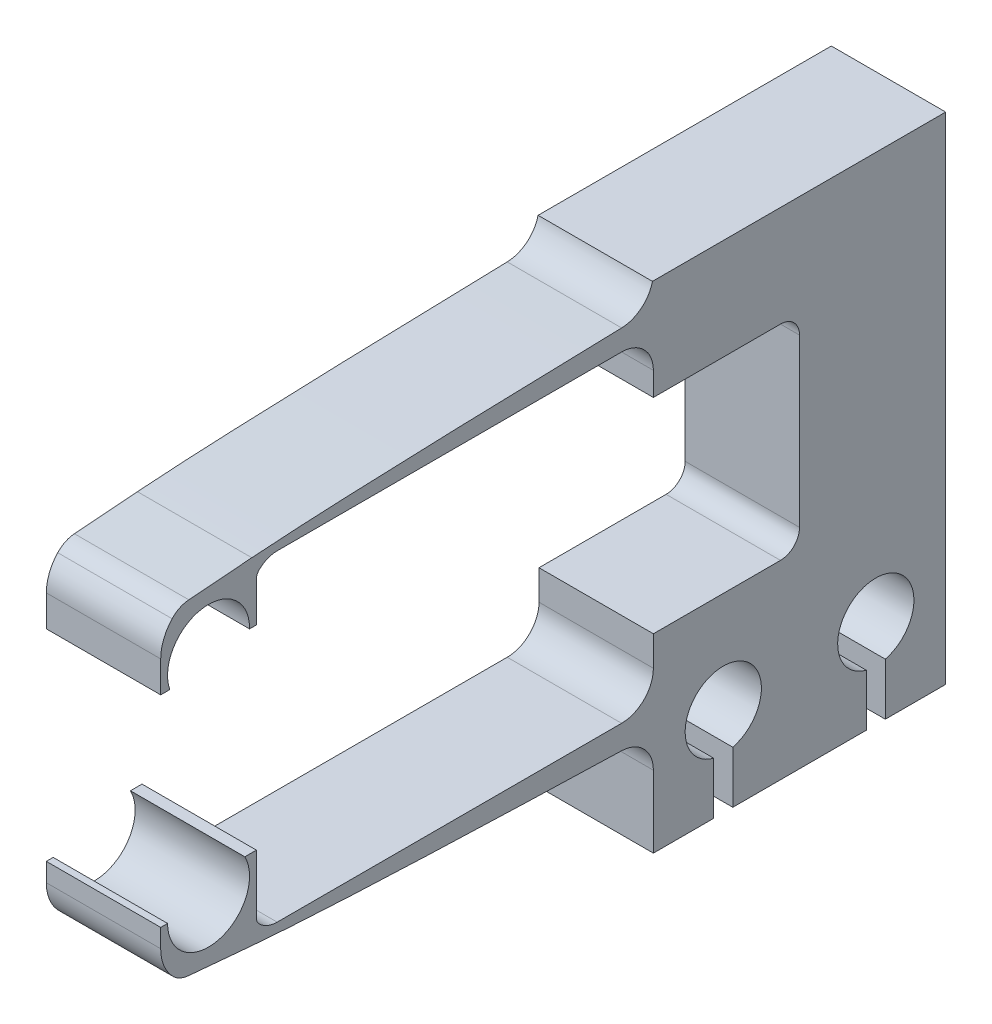
SolidWorks part; units mm, degrees
material "Titanium"
ref_plane "Front" through (0, 0, 0) normal (0, 0, 1) x (1, 0, 0)
ref_plane "Top" through (0, 0, 0) normal (0, 1, 0) x (1, 0, 0)
ref_plane "Right" through (0, 0, 0) normal (1, 0, 0) x (0, 0, -1)
sketch "Sketch1" plane through (0, 0, 0) normal (1, 0, 0) x (0, 0, -1)
  line L0 (0, 0) -> (23.25, 0) construction
  line L1 (1.7, 6.2) -> (16.25, 6.2) construction
  line L2 (-1.7, -4.45) -> (-1.7, -6.45) construction
  line L3 (0, -6.45) -> (-1.7, -6.45) construction
  line L4 (41.8092, -4.5) -> (-22.3482, -4.5) construction
  line L6 (43.4192, 4.5) -> (-21.0309, 4.5) construction
  line L7 (17.5, 4.025) -> (17.5, 4.95)
  line L8 (0, -2.75) -> (0, 2.5) construction
  line L9 (17.5, -5.2) -> (17.5, -8.6732)
  line L10 (17.5, -4.025) -> (17.5, -5.2)
  line L11 (-1.7, 4.2) -> (-1.7, 6.2) construction
  line L12 (1.7, -4.45) -> (1.7, -6.45) construction
  line L13 (1.7, -6.45) -> (16.25, -6.45) construction
  line L14 (16.25, -6.45) -> (16.25, -7.3867) construction
  line L15 (17.5, 8.5) -> (29, 8.5)
  line L16 (-1.7, 6.2) -> (0, 6.2) construction
  line L17 (29, -11.5) -> (17.5, -11.5)
  line L18 (1.7, 4.2) -> (1.7, 6.2) construction
  line L19 (17.5, 8.3014) -> (17.5, 8.5)
  line L20 (17.5, 4.95) -> (17.5, 8.3014)
  line L21 (17.5, -4.025) -> (23.25, -4.025)
  line L25 (17.5, -8.6732) -> (17.5, -11.5)
  line L26 (29, 8.5) -> (29, -11.5)
  line L27 (23.25, 0) -> (29, 0) construction
  line L29 (0, -4.45) -> (0, -6.45) construction
  line L30 (23.25, -4.025) -> (23.25, 4.025)
  line L31 (23.25, 4.025) -> (17.5, 4.025)
  arc A1 (16.25, -6.45) -> (17.5, -5.2) centre (16.25, -5.2) ccw construction
  arc A2 (-1.7, -4.45) -> (1.7, -4.45) centre (0, -4.45) cw construction
  arc A3 (1.7, 4.2) -> (-1.7, 4.2) centre (0, 4.2) cw construction
  arc A4 (16.25, 6.2) -> (17.5, 4.95) centre (16.25, 4.95) cw construction
  arc A5 (16.25, -7.3867) -> (17.5, -8.6732) centre (16.2129, -8.6732) cw construction
  arc A9 (16.25, 7.0194) -> (17.5, 8.3014) centre (16.2177, 8.3014) ccw construction
  spline S0 degree 4 poles (17.8857, -7.4327) (17.7428, -7.4287) (17.6099, -7.4252) (17.1374, -7.412) (16.4075, -7.3913) (15.697, -7.3708) (14.3979, -7.3322) (13.3617, -7.2996) (12.1009, -7.2589) (10.9759, -7.2202) (9.7686, -7.1769) (8.6115, -7.1325) (7.424, -7.084) (6.2553, -7.0321) (5.0754, -6.975) (3.903, -6.9111) (2.7276, -6.8374) (1.7227, -6.7597) (0.9543, -6.6832) (0.4564, -6.6106) (0.2371, -6.5651) (0.1371, -6.537) (0.0873, -6.5192) (0.0601, -6.5073) (0.043, -6.4984) (0.0307, -6.4909) (0.016, -6.4805) (0.0052, -6.4697) (0.0008, -6.459) (0, -6.45) knots 0 0 0 0 0 0.022654 0.045309 0.090617 0.156222 0.221826 0.28743 0.353034 0.418638 0.484242 0.549846 0.61545 0.681055 0.746659 0.812263 0.877867 0.943221 0.971682 0.984223 0.9901 0.993094 0.99484 0.995992 0.996719 0.997393 0.99806 1 1 1 1 1 construction
  spline S1 degree 4 poles (16.25, -7.3867) (15.9825, -7.379) (15.4539, -7.3636) (14.3979, -7.3322) (13.3617, -7.2996) (12.1009, -7.2589) (10.9759, -7.2202) (9.7686, -7.1769) (8.6115, -7.1325) (7.424, -7.084) (6.2553, -7.0321) (5.0754, -6.975) (3.903, -6.9111) (2.7276, -6.8374) (1.7227, -6.7597) (0.9543, -6.6832) (0.4564, -6.6106) (0.2371, -6.5651) (0.1371, -6.537) (0.0873, -6.5192) (0.0601, -6.5073) (0.043, -6.4984) (0.0307, -6.4909) (0.016, -6.4805) (0.0052, -6.4697) (0.0008, -6.459) (0, -6.45) knots 0.090617 0.090617 0.090617 0.090617 0.090617 0.156222 0.221826 0.28743 0.353034 0.418638 0.484242 0.549846 0.61545 0.681055 0.746659 0.812263 0.877867 0.943221 0.971682 0.984223 0.9901 0.993094 0.99484 0.995992 0.996719 0.997393 0.99806 1 1 1 1 1 construction
  spline S2 degree 4 poles (17.8845, 7.0597) (17.7463, 7.0563) (17.6049, 7.053) (17.143, 7.0417) (16.4101, 7.0236) (15.7139, 7.0059) (14.431, 6.9726) (13.4161, 6.9447) (12.1774, 6.9098) (11.0741, 6.8767) (9.8887, 6.8398) (8.7532, 6.8019) (7.5875, 6.7607) (6.4405, 6.7167) (5.2822, 6.6684) (4.1313, 6.6148) (2.9761, 6.5533) (1.9352, 6.4867) (1.1121, 6.4193) (0.5505, 6.3551) (0.2629, 6.3064) (0.1449, 6.2783) (0.0901, 6.2616) (0.0611, 6.2506) (0.0435, 6.2426) (0.031, 6.236) (0.0166, 6.227) (0.0056, 6.2178) (0.001, 6.2082) (0, 6.2) knots 0 0 0 0 0 0.02267 0.045339 0.090679 0.155107 0.219536 0.283964 0.348393 0.412821 0.47725 0.541678 0.606107 0.670535 0.734964 0.799392 0.863821 0.928249 0.967999 0.98346 0.99001 0.993269 0.995073 0.996228 0.996923 0.997583 0.998234 1 1 1 1 1 construction
  spline S3 degree 4 poles (16.25, 7.0194) (15.9875, 7.0128) (15.4701, 6.9996) (14.431, 6.9726) (13.4161, 6.9447) (12.1774, 6.9098) (11.0741, 6.8767) (9.8887, 6.8398) (8.7532, 6.8019) (7.5875, 6.7607) (6.4405, 6.7167) (5.2822, 6.6684) (4.1313, 6.6148) (2.9761, 6.5533) (1.9352, 6.4867) (1.1121, 6.4193) (0.5505, 6.3551) (0.2629, 6.3064) (0.1449, 6.2783) (0.0901, 6.2616) (0.0611, 6.2506) (0.0435, 6.2426) (0.031, 6.236) (0.0166, 6.227) (0.0056, 6.2178) (0.001, 6.2082) (0, 6.2) knots 0.090679 0.090679 0.090679 0.090679 0.090679 0.155107 0.219536 0.283964 0.348393 0.412821 0.47725 0.541678 0.606107 0.670535 0.734964 0.799392 0.863821 0.928249 0.967999 0.98346 0.99001 0.993269 0.995073 0.996228 0.996923 0.997583 0.998234 1 1 1 1 1 construction
  point P26 (0, -0.125)
  dimension "D7" = 1.75
  dimension "D13" = 8.05
  dimension "D14" = 2
  dimension "D2" = 1.7
  dimension "D9" = 8.5
  dimension "D11" = 4.5
  dimension "D12" = 4.5
  dimension "D8" = 5.75
  dimension "D4" = 17.5
  dimension "D3" = 2
  dimension "D5" = 23.25
  dimension "D6" = 16.25
  dimension "D10" = 11.5
  dimension "D15" = 2
  dimension "D16" = 16.25
extrude "Boss-Extrude1" add sketch "Sketch1" along normal mid plane 4.5
sketch "Sketch4" plane through (-2.25, 0, 0) normal (-1, 0, 0) x (0, 0, 1)
  line L0 (-26.625, -11.5) -> (-26.625, -9.4524)
  line L1 (-17.5, -11.5) -> (-29, -11.5) construction
  line L2 (-26.625, -11.5) -> (-25.875, -11.5)
  line L3 (-25.875, -11.5) -> (-25.875, -9.4524)
  line L4 (-20.625, -9.4524) -> (-20.625, -11.5)
  line L5 (-20.625, -11.5) -> (-19.875, -11.5)
  line L6 (-19.875, -11.5) -> (-19.875, -9.4524)
  line L7 (-26.625, -9.4524) -> (-25.875, -9.4524) construction
  line L8 (-20.625, -9.4524) -> (-19.875, -9.4524) construction
  line L9 (-20.25, -8) -> (-26.25, -8) construction
  line L10 (-26.25, -8) -> (-26.25, 0) construction
  line L11 (-26.25, 0) -> (-23.25, 0) construction
  line L12 (-23.25, 4.025) -> (-23.25, -4.025) construction
  line L13 (-17.5, -4.025) -> (-17.5, -11.5) construction
  line L14 (-29, -11.5) -> (-29, 8.5) construction
  arc A0 (-26.625, -9.4524) -> (-25.875, -9.4524) centre (-26.25, -8) cw
  arc A1 (-20.625, -9.4524) -> (-19.875, -9.4524) centre (-20.25, -8) cw
  dimension "D5" = 1.5
  dimension "D1" = 0.75
  dimension "D2" = 3
  dimension "D3" = 8
  dimension "D4" = 6
  dimension "D6" = 2.75
  dimension "D7" = 2.75
extrude "Cut-Extrude1" cut sketch "Sketch4" against normal through all
fillet "Fillet1" radius 0.75 2 edges at (0, -4.025, -23.25) (0, 4.025, -23.25)
sketch "Sketch2" plane through (0, 0, 0) normal (1, 0, 0) x (0, 0, -1)
  line L0 (1.7, -6.45) -> (16.25, -6.45) construction
  line L1 (1.7, -4.45) -> (1.7, -6.45) construction
  line L2 (-1.7, -4.45) -> (-1.7, -6.45) construction
  line L3 (0, -6.45) -> (-1.7, -6.45) construction
  line L5 (1.7, -6.45) -> (16.25, -6.45)
  line L6 (1.7, -4.45) -> (1.7, -6.45)
  line L7 (-1.7, -4.45) -> (-1.7, -6.45)
  line L8 (0, -6.45) -> (-1.7, -6.45)
  line L9 (17.5, -5.2) -> (17.5, -8.6732) construction
  line L11 (17.5, -5.2) -> (17.5, -8.6732)
  line L12 (17.5, 4.95) -> (17.5, 8.3014) construction
  line L13 (1.7, 6.2) -> (16.25, 6.2) construction
  line L14 (-1.7, 6.2) -> (0, 6.2) construction
  line L15 (-1.7, 4.2) -> (-1.7, 6.2) construction
  line L16 (1.7, 4.2) -> (1.7, 6.2) construction
  line L17 (17.5, 4.95) -> (17.5, 8.3014)
  line L18 (1.7, 6.2) -> (16.25, 6.2)
  line L19 (-1.7, 6.2) -> (0, 6.2)
  line L20 (-1.7, 4.2) -> (-1.7, 6.2)
  line L21 (1.7, 4.2) -> (1.7, 6.2)
  arc A0 (1.7, -4.45) -> (-1.7, -4.45) centre (0, -4.45) ccw construction
  arc A3 (1.7, -4.45) -> (-1.7, -4.45) centre (0, -4.45) ccw
  arc A4 (17.5, -8.6732) -> (16.25, -7.3867) centre (16.2129, -8.6732) ccw construction
  arc A5 (16.25, -6.45) -> (17.5, -5.2) centre (16.25, -5.2) ccw construction
  arc A6 (16.25, -6.45) -> (17.5, -5.2) centre (16.25, -5.2) ccw
  arc A7 (17.5, -8.6732) -> (16.25, -7.3867) centre (16.2129, -8.6732) ccw
  arc A8 (16.25, 7.0194) -> (17.5, 8.3014) centre (16.2177, 8.3014) ccw construction
  arc A9 (17.5, 4.95) -> (16.25, 6.2) centre (16.25, 4.95) ccw construction
  arc A10 (-1.7, 4.2) -> (1.7, 4.2) centre (0, 4.2) ccw construction
  arc A11 (16.25, 7.0194) -> (17.5, 8.3014) centre (16.2177, 8.3014) ccw
  arc A12 (17.5, 4.95) -> (16.25, 6.2) centre (16.25, 4.95) ccw
  arc A13 (-1.7, 4.2) -> (1.7, 4.2) centre (0, 4.2) ccw
  spline S0 degree 4 poles (1015.806, -36.1419) (-25.1587, -6.1713) (25.4391, -7.6458) (16.9585, -7.4127) (13.3617, -7.2996) (12.1009, -7.2589) (10.9759, -7.2202) (9.7686, -7.1769) (8.6115, -7.1325) (7.424, -7.084) (6.2553, -7.0321) (5.0754, -6.975) (3.903, -6.9111) (2.7276, -6.8374) (1.7227, -6.7597) (0.9543, -6.6832) (0.4564, -6.6106) (0.2371, -6.5651) (0.1371, -6.537) (0.0873, -6.5192) (0.0601, -6.5073) (0.043, -6.4984) (0.0307, -6.4909) (-0.1968, -6.3287) (0.0146, -5.4129) (43.0294, 6.1836) (-939.7828, -347.8084) knots -0.557828 -0.557828 -0.557828 -0.557828 -0.557828 0.156222 0.221826 0.28743 0.353034 0.418638 0.484242 0.549846 0.61545 0.681055 0.746659 0.812263 0.877867 0.943221 0.971682 0.984223 0.9901 0.993094 0.99484 0.995992 0.996719 0.997393 0.99806 1.058105 1.058105 1.058105 1.058105 1.058105 only from (16.25, -7.3867) to (0, -6.45) construction
  spline S1 degree 4 poles (16.25, -7.3867) (15.9825, -7.379) (15.4539, -7.3636) (14.3979, -7.3322) (13.3617, -7.2996) (12.1009, -7.2589) (10.9759, -7.2202) (9.7686, -7.1769) (8.6115, -7.1325) (7.424, -7.084) (6.2553, -7.0321) (5.0754, -6.975) (3.903, -6.9111) (2.7276, -6.8374) (1.7227, -6.7597) (0.9543, -6.6832) (0.4564, -6.6106) (0.2371, -6.5651) (0.1371, -6.537) (0.0873, -6.5192) (0.0601, -6.5073) (0.043, -6.4984) (0.0307, -6.4909) (0.016, -6.4805) (0.0052, -6.4697) (0.0008, -6.459) (0, -6.45) knots 0.090617 0.090617 0.090617 0.090617 0.090617 0.156222 0.221826 0.28743 0.353034 0.418638 0.484242 0.549846 0.61545 0.681055 0.746659 0.812263 0.877867 0.943221 0.971682 0.984223 0.9901 0.993094 0.99484 0.995992 0.996719 0.997393 0.99806 1 1 1 1 1
  spline S2 degree 4 poles (1015.9078, 32.1833) (-25.0126, 5.9604) (25.309, 7.2431) (16.9336, 7.0414) (13.4161, 6.9447) (12.1774, 6.9098) (11.0741, 6.8767) (9.8887, 6.8398) (8.7532, 6.8019) (7.5875, 6.7607) (6.4405, 6.7167) (5.2822, 6.6684) (4.1313, 6.6148) (2.9761, 6.5533) (1.9352, 6.4867) (1.1121, 6.4193) (0.5505, 6.3551) (0.2629, 6.3064) (0.1449, 6.2783) (0.0901, 6.2616) (0.0611, 6.2506) (0.0435, 6.2426) (0.031, 6.236) (-0.1871, 6.1007) (-0.1475, 5.3114) (43.6109, -10.4306) (-899.4391, 442.7049) knots -0.544854 -0.544854 -0.544854 -0.544854 -0.544854 0.155107 0.219536 0.283964 0.348393 0.412821 0.47725 0.541678 0.606107 0.670535 0.734964 0.799392 0.863821 0.928249 0.967999 0.98346 0.99001 0.993269 0.995073 0.996228 0.996923 0.997583 0.998234 1.053425 1.053425 1.053425 1.053425 1.053425 only from (16.25, 7.0194) to (0, 6.2) construction
  spline S3 degree 4 poles (16.25, 7.0194) (15.9875, 7.0128) (15.4701, 6.9996) (14.431, 6.9726) (13.4161, 6.9447) (12.1774, 6.9098) (11.0741, 6.8767) (9.8887, 6.8398) (8.7532, 6.8019) (7.5875, 6.7607) (6.4405, 6.7167) (5.2822, 6.6684) (4.1313, 6.6148) (2.9761, 6.5533) (1.9352, 6.4867) (1.1121, 6.4193) (0.5505, 6.3551) (0.2629, 6.3064) (0.1449, 6.2783) (0.0901, 6.2616) (0.0611, 6.2506) (0.0435, 6.2426) (0.031, 6.236) (0.0166, 6.227) (0.0056, 6.2178) (0.001, 6.2082) (0, 6.2) knots 0.090679 0.090679 0.090679 0.090679 0.090679 0.155107 0.219536 0.283964 0.348393 0.412821 0.47725 0.541678 0.606107 0.670535 0.734964 0.799392 0.863821 0.928249 0.967999 0.98346 0.99001 0.993269 0.995073 0.996228 0.996923 0.997583 0.998234 1 1 1 1 1
extrude "Boss-Extrude2" add sketch "Sketch2" along normal mid plane 4.5
sketch "Sketch3" plane through (-2.25, 0, 0) normal (-1, 0, 0) x (0, 0, 1)
  line L0 (1.7, -6.45) -> (-1.6908, -6.7522)
  line L1 (1.7, -6.45) -> (0, -6.45) construction
  line L2 (1.7, -6.45) -> (0, -6.45)
  line L3 (0, 6.2) -> (1.7, 6.2) construction
  line L4 (0, 6.2) -> (1.7, 6.2)
  line L5 (1.7, 6.2) -> (-1.7017, 6.4652)
  spline S0 degree 4 poles (939.596, -347.7411) (-43.0233, 6.1819) (-0.0146, -5.413) (0.1968, -6.3287) (-0.0307, -6.4909) (-0.043, -6.4984) (-0.0601, -6.5073) (-0.0873, -6.5192) (-0.1371, -6.537) (-0.2371, -6.5651) (-0.4564, -6.6106) (-0.9543, -6.6832) (-1.7227, -6.7597) (-2.7276, -6.8374) (-3.903, -6.9111) (-5.0754, -6.975) (-6.2553, -7.0321) (-7.424, -7.084) (-8.6115, -7.1325) (-9.7686, -7.1769) (-10.9759, -7.2202) (-12.1009, -7.2589) (-13.3617, -7.2996) (-16.9585, -7.4127) (-25.4391, -7.6458) (25.1593, -6.1713) (-1015.825, -36.1424) knots 0.032516 0.032516 0.032516 0.032516 0.032516 0.092558 0.093225 0.093899 0.094625 0.095777 0.097523 0.100517 0.106395 0.118935 0.147397 0.212751 0.278355 0.343959 0.409563 0.475167 0.540771 0.606375 0.671979 0.737584 0.803188 0.868792 0.934396 1.648448 1.648448 1.648448 1.648448 1.648448 only from (0, -6.45) to (-16.25, -7.3867) construction
  spline S1 degree 4 poles (0, -6.45) (-0.0008, -6.459) (-0.0052, -6.4697) (-0.016, -6.4805) (-0.0307, -6.4909) (-0.043, -6.4984) (-0.0601, -6.5073) (-0.0873, -6.5192) (-0.1371, -6.537) (-0.2371, -6.5651) (-0.4564, -6.6106) (-0.8426, -6.6669) (-1.2048, -6.7069) (-1.5113, -6.7362) (-1.6908, -6.7522) knots 0.090617 0.090617 0.090617 0.090617 0.090617 0.092558 0.093225 0.093899 0.094625 0.095777 0.097523 0.100517 0.106395 0.118935 0.147397 0.187581 0.187581 0.187581 0.187581 0.187581
  spline S2 degree 4 poles (0, -6.45) (-0.0008, -6.459) (-0.0052, -6.4697) (-0.016, -6.4805) (-0.0307, -6.4909) (-0.043, -6.4984) (-0.0601, -6.5073) (-0.0873, -6.5192) (-0.1371, -6.537) (-0.2371, -6.5651) (-0.4564, -6.6106) (-0.9543, -6.6832) (-1.7227, -6.7597) (-2.7276, -6.8374) (-3.903, -6.9111) (-5.0754, -6.975) (-6.2553, -7.0321) (-7.424, -7.084) (-8.6115, -7.1325) (-9.7686, -7.1769) (-10.9759, -7.2202) (-12.1009, -7.2589) (-13.3617, -7.2996) (-14.3979, -7.3322) (-15.4539, -7.3636) (-15.9825, -7.379) (-16.25, -7.3867) knots 0.090617 0.090617 0.090617 0.090617 0.090617 0.092558 0.093225 0.093899 0.094625 0.095777 0.097523 0.100517 0.106395 0.118935 0.147397 0.212751 0.278355 0.343959 0.409563 0.475167 0.540771 0.606375 0.671979 0.737584 0.803188 0.868792 0.934396 1 1 1 1 1 construction
  spline S3 degree 4 poles (-1015.9078, 32.1833) (25.0126, 5.9604) (-25.309, 7.2431) (-16.9336, 7.0414) (-13.4161, 6.9447) (-12.1774, 6.9098) (-11.0741, 6.8767) (-9.8887, 6.8398) (-8.7532, 6.8019) (-7.5875, 6.7607) (-6.4405, 6.7167) (-5.2822, 6.6684) (-4.1313, 6.6148) (-2.9761, 6.5533) (-1.9352, 6.4867) (-1.1121, 6.4193) (-0.5505, 6.3551) (-0.2629, 6.3064) (-0.1449, 6.2783) (-0.0901, 6.2616) (-0.0611, 6.2506) (-0.0435, 6.2426) (-0.031, 6.236) (0.1871, 6.1007) (0.1475, 5.3114) (-43.6109, -10.4306) (899.4391, 442.7049) knots -0.544854 -0.544854 -0.544854 -0.544854 -0.544854 0.155107 0.219536 0.283964 0.348393 0.412821 0.47725 0.541678 0.606107 0.670535 0.734964 0.799392 0.863821 0.928249 0.967999 0.98346 0.99001 0.993269 0.995073 0.996228 0.996923 0.997583 0.998234 1.053425 1.053425 1.053425 1.053425 1.053425 only from (-16.25, 7.0194) to (0, 6.2) construction
  spline S4 degree 4 poles (-1.7017, 6.4652) (-1.5885, 6.4564) (-1.2977, 6.4327) (-0.9381, 6.3994) (-0.5505, 6.3551) (-0.2629, 6.3064) (-0.1449, 6.2783) (-0.0901, 6.2616) (-0.0611, 6.2506) (-0.0435, 6.2426) (-0.031, 6.236) (-0.0166, 6.227) (-0.0056, 6.2178) (-0.001, 6.2082) (0, 6.2) knots 0.902915 0.902915 0.902915 0.902915 0.902915 0.928249 0.967999 0.98346 0.99001 0.993269 0.995073 0.996228 0.996923 0.997583 0.998234 1 1 1 1 1
extrude "Boss-Extrude4" add sketch "Sketch3" against normal through all
fillet "Fillet2" radius 1 4 edges at (0, -6.45, -1.7) (0, -6.45, 1.7) (0, 6.2, 1.7) (0, 6.2, -1.7)
sketch "Sketch6" plane through (0, 0, 0) normal (1, 0, 0) x (0, 0, -1)
  line L0 (-1.6125, -4.3375) -> (-1.6963, -4.3375)
  line L1 (-1.6963, -4.3375) -> (-1.6963, -2.65)
  line L2 (-1.6963, -2.65) -> (1.6963, -2.65)
  line L3 (1.6963, -2.65) -> (1.6963, -4.3375)
  line L4 (1.6963, -4.3375) -> (1.6125, -4.3375)
  line L5 (0, -2.75) -> (0, -2.65) construction
  line L6 (1.6122, 4.0837) -> (1.696, 4.0837)
  line L7 (1.696, 4.0837) -> (1.696, 2.3962)
  line L8 (1.696, 2.3962) -> (-1.696, 2.3962)
  line L9 (-1.696, 2.3962) -> (-1.696, 4.0837)
  line L10 (-1.696, 4.0837) -> (-1.6122, 4.0837)
  line L11 (0, -4.3375) -> (0, -4.45) construction
  arc A0 (1.6122, 4.0837) -> (-1.6122, 4.0837) centre (0, 4.1125) ccw
  arc A1 (-1.6125, -4.3375) -> (1.6125, -4.3375) centre (0, -4.3375) ccw
  arc A2 (1.7, -4.45) -> (-1.7, -4.45) centre (0, -4.45) ccw construction
  arc A3 (-1.7, 4.2) -> (1.7, 4.2) centre (0, 4.2) ccw construction
  circle A4 centre (0, -4.3375) radius 1.5875 construction
  point P7 (0, -2.75)
  point P9 (0, 2.5)
  dimension "D1" = 0.025
  dimension "D3" = 3.175
  dimension "D2" = 0.1
  dimension "D4" = 0.0838
extrude "Cut-Extrude4" cut sketch "Sketch6" against normal mid plane 10
sketch "Sketch5" [suppressed] plane through (-2.25, 0, 0) normal (-1, 0, 0) x (0, 0, 1)
  line L1 (-18.5, 0) -> (31.5, 0)
  line L2 (-18.5, 0) -> (-18.5, -11.5)
  line L3 (-18.5, -11.5) -> (31.5, -11.5)
  line L4 (31.5, 0) -> (31.5, -11.5)
  dimension "D1" = 50
sketch "Sketch9" plane through (0, 0, 0) normal (1, 0, 0) x (0, 0, -1)
  line L0 (1.6963, -4.3375) -> (1.8825, -4.3375) construction
  line L1 (-1.6963, -4.3375) -> (-1.8825, -4.3375)
  line L2 (1.8825, -4.3375) -> (1.8825, -5.8906)
  line L3 (-1.8825, -4.3375) -> (-1.8825, -5.0653)
  line L4 (1.7, -5.45) -> (1.7, -4.45) construction
  line L5 (-1.7, -4.45) -> (-1.7, -5.5351) construction
  line L6 (1.7, -5.45) -> (1.7, -4.45)
  line L7 (-1.7, -4.45) -> (-1.7, -5.5351)
  line L8 (1.6125, -4.3375) -> (1.8825, -4.3375) construction
  line L9 (1.696, 4.0837) -> (1.8822, 4.0837)
  line L10 (1.8822, 4.0837) -> (1.8822, 5.64)
  line L11 (-1.696, 4.0837) -> (-1.8822, 4.0837) construction
  line L12 (-1.8822, 4.0837) -> (-1.8822, 4.8096)
  line L13 (1.7, 4.2) -> (1.7, 5.2) construction
  line L14 (-1.7, 5.2749) -> (-1.7, 4.2) construction
  line L15 (1.7, 4.2) -> (1.7, 5.2)
  line L16 (-1.7, 5.2749) -> (-1.7, 4.2)
  line L17 (1.8825, -4.3375) -> (1.8825, -3.5875)
  line L18 (1.8825, -3.5875) -> (1.4275, -3.5875)
  line L19 (-1.8822, 4.0837) -> (-1.8822, 3.5837)
  line L20 (-1.8822, 3.5837) -> (-1.5233, 3.5837)
  line L21 (-1.6122, 4.0837) -> (-1.696, 4.0837)
  line L22 (1.6963, -4.3375) -> (1.6125, -4.3375)
  line L23 (-1.8822, 3.5837) -> (-0.9903, 2.8718) construction
  arc A0 (-1.8825, -5.0653) -> (-1.4378, -6.2101) centre (-0.1864, -5.0653) ccw
  arc A1 (-1.7, -5.5351) -> (-0.7888, -6.5312) centre (-0.7, -5.5351) ccw construction
  arc A2 (1.8825, -5.8906) -> (1.9929, -6.1571) centre (2.2594, -5.8906) ccw
  arc A3 (1.7, -5.45) -> (2.7, -6.45) centre (2.7, -5.45) ccw construction
  arc A4 (1.7, -4.45) -> (1.6963, -4.3375) centre (0, -4.45) ccw construction
  arc A5 (-1.6963, -4.3375) -> (-1.7, -4.45) centre (0, -4.45) ccw construction
  arc A6 (1.7, -4.45) -> (1.6963, -4.3375) centre (0, -4.45) ccw
  arc A7 (1.7, -5.45) -> (1.9929, -6.1571) centre (2.7, -5.45) ccw
  arc A8 (-1.6963, -4.3375) -> (-1.7, -4.45) centre (0, -4.45) ccw
  arc A9 (-1.7, -5.5351) -> (-1.4378, -6.2101) centre (-0.7, -5.5351) ccw
  arc A10 (-1.6125, -4.3375) -> (1.6125, -4.3375) centre (0, -4.3375) ccw construction
  arc A11 (-1.4341, 5.954) -> (-1.8822, 4.8096) centre (-0.1969, 4.8096) ccw
  arc A12 (-0.7777, 6.2719) -> (-1.7, 5.2749) centre (-0.7, 5.2749) ccw construction
  arc A13 (1.8822, 5.64) -> (1.9929, 5.9071) centre (2.26, 5.64) cw
  arc A14 (2.7, 6.2) -> (1.7, 5.2) centre (2.7, 5.2) ccw construction
  arc A15 (1.696, 4.0837) -> (1.7, 4.2) centre (0, 4.2) ccw construction
  arc A16 (-1.7, 4.2) -> (-1.696, 4.0837) centre (0, 4.2) ccw construction
  arc A17 (1.696, 4.0837) -> (1.7, 4.2) centre (0, 4.2) ccw
  arc A18 (1.9929, 5.9071) -> (1.7, 5.2) centre (2.7, 5.2) ccw
  arc A19 (-1.7, 4.2) -> (-1.696, 4.0837) centre (0, 4.2) ccw
  arc A20 (-1.4341, 5.954) -> (-1.7, 5.2749) centre (-0.7, 5.2749) ccw
  arc A21 (1.4275, -3.5875) -> (1.6125, -4.3375) centre (0, -4.3375) cw
  arc A22 (-1.6122, 4.0837) -> (-1.5233, 3.5837) centre (0, 4.1125) ccw
  arc A23 (1.6122, 4.0837) -> (-1.6122, 4.0837) centre (0, 4.1125) ccw construction
  circle A24 centre (0, 4.1125) radius 1.5875 construction
  dimension "D5" = 3.175
  dimension "D1" = 0.27
  dimension "D2" = 0.75
  dimension "D3" = 0.5
  dimension "D4" = 38.596
extrude "Boss-Extrude5" add sketch "Sketch9" along normal up to surface and the other way up to surface
sketch "Sketch12" plane through (-2.25, 0, 0) normal (-1, 0, 0) x (0, 0, 1)
  line L1 (-29, 8.5) -> (-17.4641, 8.5)
  line L2 (-29, 8.5) -> (-29, 8)
  line L3 (-29, 8) -> (-17.4641, 8)
  line L4 (-17.4641, 8.5) -> (-17.4641, 8)
  arc A0 (-17.5, 8.3014) -> (-16.25, 7.0194) centre (-16.2177, 8.3014) ccw construction
  dimension "D1" = 0.5
extrude "Cut-Extrude5" cut sketch "Sketch12" against normal through all
extrude "Cut-Extrude2" [suppressed] cut sketch "Sketch5" against normal through all
sketch "Sketch11" [suppressed] plane through (0, 0, 0) normal (1, 0, 0) x (0, 0, -1)
  line L0 (1.8822, 4.0837) -> (1.3255, 3.2389)
  line L1 (1.3255, 3.2389) -> (1.3255, 4.1125)
  circle A0 centre (0, 4.1125) radius 1.5875
  circle A2 centre (0, -4.3375) radius 1.5875 construction
  dimension "D1" = 33.386
equation "\"ball_diameter\"= 5/32*25.4"
equation "\"mega\"= 1e6"
equation "\"milli\"= 1e-3"
equation "\"width\"= 4.5"
equation "\"max_stress_ratio\"= 0.5"
equation "\"yield_stress\"= 880"
equation "\"modulus\"= 113"
equation "\"k1_defl\"= 2    'The top spring, which drives ball into groove."
equation "\"k1_force\"= 15"
equation "\"k1_beam_length\"= 3/2 / (\"max_stress_ratio\"*\"yield_stress\"*\"mega\") * (4/5 * \"modulus\"*1e9 * (1.15*\"k1_defl\"*\"milli\"))^(2/3)*(\"k1_force\"/(\"width\"*\"milli\"))^(1/3)/\"milli\""
equation "\"k2_defl\"= 1.5    'The bottom spring, which (when present) supports the hanging mass."
equation "\"k2_force\"= 24.5"
equation "\"k2_beam_length\"= 3/2 / (\"max_stress_ratio\"*\"yield_stress\"*\"mega\") * (4/5 * \"modulus\"*1e9 * (1.15*\"k2_defl\"*\"milli\"))^(2/3)*(\"k2_force\"/(\"width\"*\"milli\"))^(1/3)/\"milli\""
